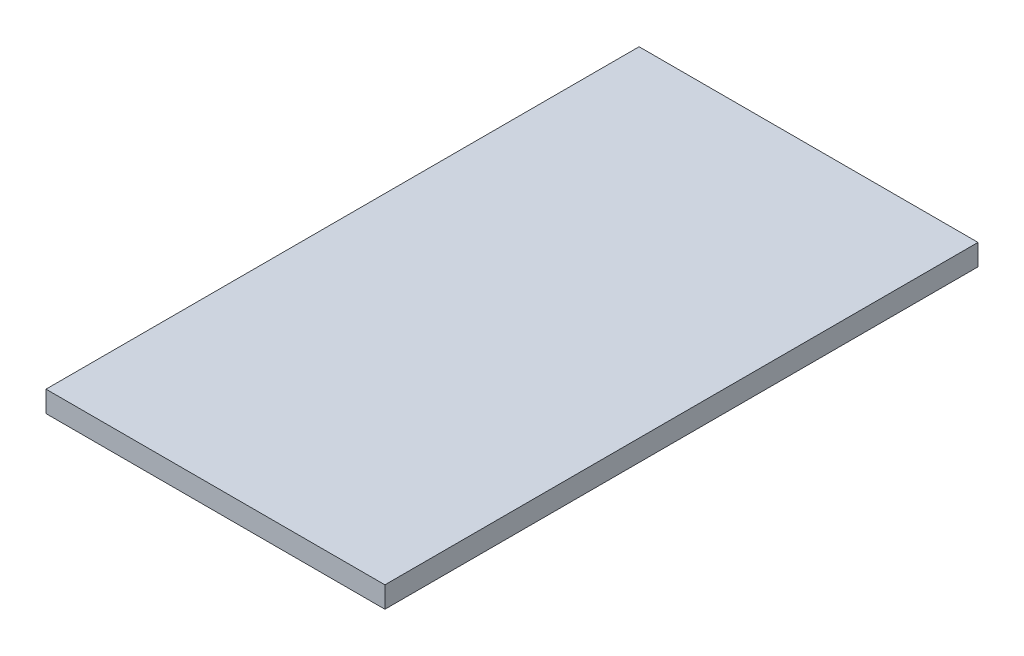
SolidWorks part; units mm, degrees
ref_plane "Front Plane" through (0, 0, 0) normal (0, 0, 1) x (1, 0, 0)
ref_plane "Top Plane" through (0, 0, 0) normal (0, 1, 0) x (1, 0, 0)
ref_plane "Right Plane" through (0, 0, 0) normal (1, 0, 0) x (0, 0, -1)
sketch "Sketch1" plane through (0, 0, 0) normal (0, 1, 0) x (1, 0, 0)
  line L1 (-70.2951, 43.2787) -> (89.7049, 43.2787)
  line L2 (-70.2951, 43.2787) -> (-70.2951, -236.7213)
  line L3 (-70.2951, -236.7213) -> (89.7049, -236.7213)
  line L4 (89.7049, 43.2787) -> (89.7049, -236.7213)
  dimension "D1" = 160
  dimension "D2" = 280
extrude "Boss-Extrude1" add sketch "Sketch1" along normal blind 10
